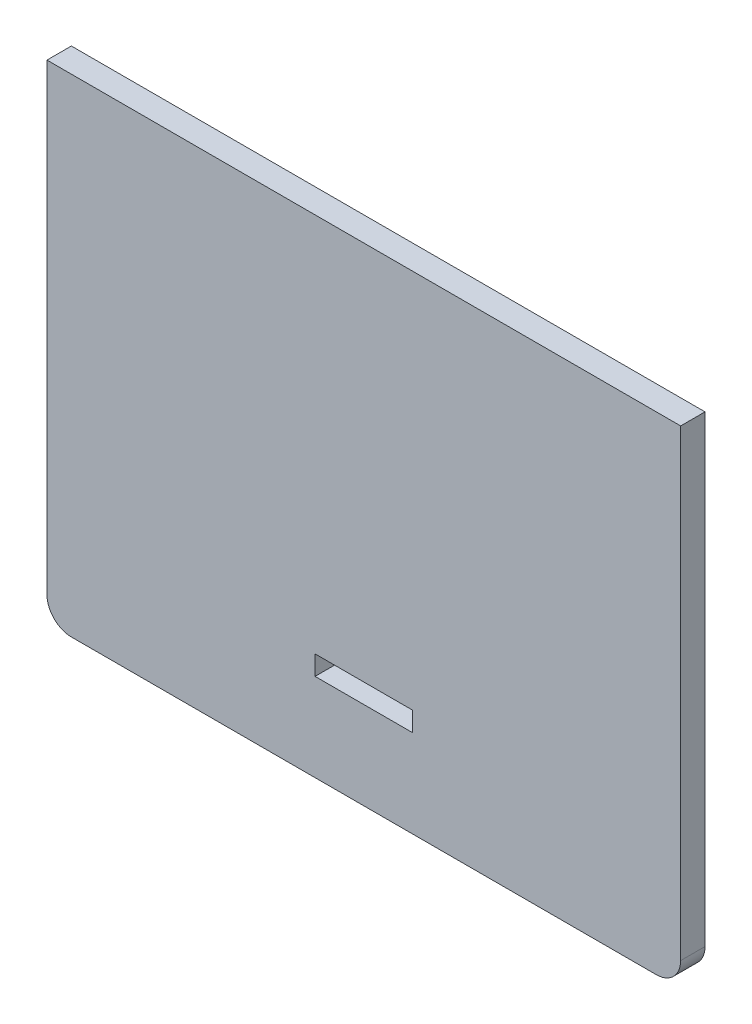
SolidWorks part; units mm, degrees
ref_plane "Front Plane" through (0, 0, 0) normal (0, 0, 1) x (1, 0, 0)
ref_plane "Top Plane" through (0, 0, 0) normal (0, 1, 0) x (1, 0, 0)
ref_plane "Right Plane" through (0, 0, 0) normal (1, 0, 0) x (0, 0, -1)
sketch "Sketch2" plane through (0, 0, 0) normal (0, 0, 1) x (1, 0, 0)
  line L1 (-65, 50) -> (65, 50)
  line L2 (-65, 50) -> (-65, -50)
  line L3 (-65, -50) -> (65, -50)
  line L4 (65, 50) -> (65, -50)
  line L5 (-65, 50) -> (65, -50) construction
  line L6 (-65, -50) -> (65, 50) construction
  point P0 (0, 0)
  dimension "D1" = 130
  dimension "D2" = 100
extrude "Boss-Extrude1" add sketch "Sketch2" along normal mid plane 5 contours L2 L1 L4 L3
fillet "Fillet1" radius 5 2 edges at (65, -50, 0) (-65, -50, 0)
sketch "Sketch3" plane through (0, 0, 2.5) normal (0, 0, 1) x (1, 0, 0)
  line L0 (0, 0) -> (0, -30) construction
  line L2 (-10, -28) -> (10, -28)
  line L3 (-10, -28) -> (-10, -32)
  line L4 (-10, -32) -> (10, -32)
  line L5 (10, -28) -> (10, -32)
  line L6 (-10, -28) -> (10, -32) construction
  line L7 (-10, -32) -> (10, -28) construction
  dimension "D1" = 30
  dimension "D2" = 4
  dimension "D3" = 20
extrude "Cut-Extrude1" cut sketch "Sketch3" against normal blind 5
